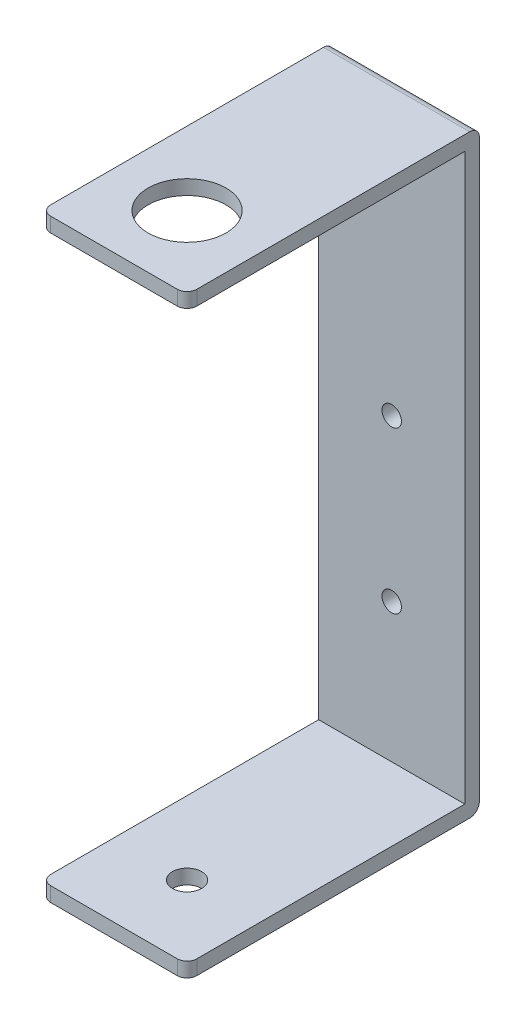
SolidWorks part; units mm, degrees
ref_plane "Front Plane" through (0, 0, 0) normal (0, 0, 1) x (1, 0, 0)
ref_plane "Top Plane" through (0, 0, 0) normal (0, 1, 0) x (1, 0, 0)
ref_plane "Right Plane" through (0, 0, 0) normal (1, 0, 0) x (0, 0, -1)
sketch "Sketch1" plane through (0, 0, 0) normal (0, 0, 1) x (1, 0, 0)
  line L1 (-7.5, -30.5) -> (7.5, -30.5)
  line L2 (-7.5, -30.5) -> (-7.5, 30.5)
  line L3 (-7.5, 30.5) -> (7.5, 30.5)
  line L4 (7.5, -30.5) -> (7.5, 30.5)
  line L5 (-7.5, -30.5) -> (7.5, 30.5) construction
  line L6 (-7.5, 30.5) -> (7.5, -30.5) construction
  line L7 (-7.5, 30.5) -> (7.5, 30.5)
  line L8 (-7.5, 30.5) -> (-7.5, 26.8473)
  line L10 (7.5, 30.5) -> (7.5, 26.8473)
  line L11 (7.5, -30.5) -> (-7.5, -30.5)
  line L12 (7.5, -30.5) -> (7.5, -23.0426)
  line L14 (-7.5, -30.5) -> (-7.5, -23.0426)
  point P0 (0, 0)
  dimension "D1" = 15
  dimension "D2" = 61
extrude "Boss-Extrude1" add sketch "Sketch1" along normal blind 1.5
sketch "Sketch2" plane through (0, 0, 1.5) normal (0, 0, 1) x (1, 0, 0)
  line L0 (7.5, -30.5) -> (7.5, 30.5) construction
  line L1 (-7.5, 30.5) -> (7.5, 30.5)
  line L2 (-7.5, 30.5) -> (-7.5, 29)
  line L3 (-7.5, 29) -> (7.5, 29)
  line L4 (7.5, 30.5) -> (7.5, 29)
  line L5 (-7.5, -30.5) -> (-7.5, 30.5) construction
  line L6 (7.5, -30.5) -> (-7.5, -30.5)
  line L7 (7.5, -30.5) -> (7.5, -29)
  line L8 (7.5, -29) -> (-7.5, -29)
  line L9 (-7.5, -30.5) -> (-7.5, -29)
  dimension "D1" = 1.5
  dimension "D2" = 1.5
extrude "Boss-Extrude2" add sketch "Sketch2" along normal blind 28.5
sketch "Sketch3" plane through (0, 30.5, 0) normal (0, 1, 0) x (1, 0, 0)
  line L0 (7.5, -30) -> (-7.5, -30) construction
  circle A0 centre (0, -22.5) radius 1.5
  dimension "D2" = 3
  dimension "D1" = 7.5
extrude "Cut-Extrude1" cut sketch "Sketch3" against normal through all
fillet "Fillet1" radius 1 6 edges at (0, -30.5, 0) (-7.5, -29.75, 30) (7.5, -29.75, 30) (7.5, 29.75, 30) (-7.5, 29.75, 30) (0, 30.5, 0)
sketch "Sketch5" plane through (0, 30.5, 0) normal (0, 1, 0) x (1, 0, 0)
  circle A0 centre (0, -22.5) radius 4
  dimension "D1" = 8
extrude "Cut-Extrude2" cut sketch "Sketch5" against normal up to next
sketch "Sketch6" plane through (0, 0, 1.5) normal (0, 0, 1) x (1, 0, 0)
  line L2 (6.5, -29) -> (-6.5, -29) construction
  circle A0 centre (0, -14.75) radius 1
  circle A1 centre (0, 1.762) radius 1
  dimension "D1" = 2
  dimension "D2" = 13.25
  dimension "D3" = 14.512
  dimension "D4" = 2
extrude "Cut-Extrude3" cut sketch "Sketch6" against normal blind 10
